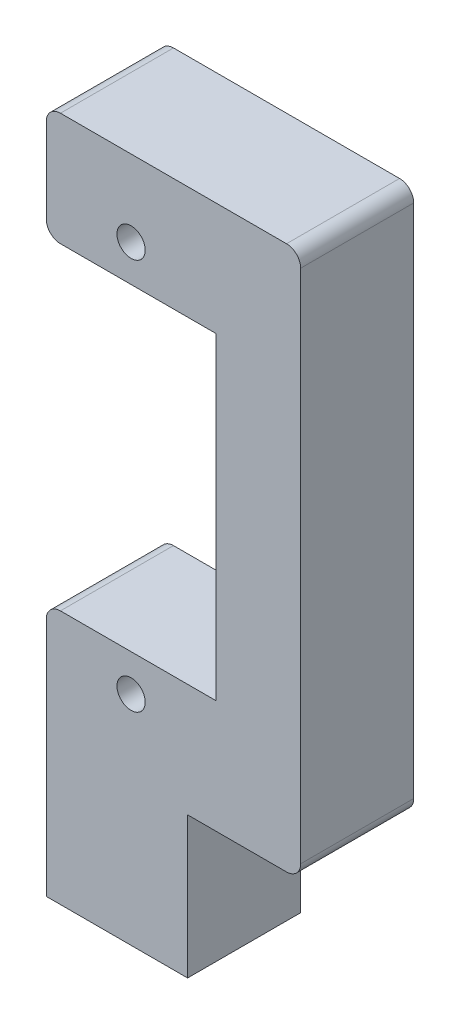
SolidWorks part; units mm, degrees
ref_plane "Front Plane" through (0, 0, 0) normal (0, 0, 1) x (1, 0, 0)
ref_plane "Top Plane" through (0, 0, 0) normal (0, 1, 0) x (1, 0, 0)
ref_plane "Right Plane" through (0, 0, 0) normal (1, 0, 0) x (0, 0, -1)
sketch "Sketch1" plane through (0, 0, 0) normal (0, 0, 1) x (1, 0, 0)
  line L0 (0, 0) -> (0, 10)
  line L1 (8, 48.5) -> (-10, 48.5)
  line L2 (-10, 48.5) -> (-10, 40.5)
  line L3 (-10, 40.5) -> (2, 40.5)
  line L4 (2, 40.5) -> (2, 18)
  line L5 (2, 18) -> (-10, 18)
  line L6 (-10, 18) -> (-10, 10)
  line L7 (0, 10) -> (8, 10)
  line L8 (-10, 10) -> (-10, 0)
  line L9 (-10, 0) -> (0, 0)
  line L10 (8, 10) -> (8, 48.5)
  line L11 (8, 29.25) -> (-17.0252, 29.25) construction
  line L12 (-4, 40.5) -> (-4, 18) construction
  circle A0 centre (-4, 43.1) radius 1
  circle A1 centre (-4, 15.4) radius 1
  dimension "D8" = 13.85
  dimension "D10" = 2
  dimension "D1" = 10
  dimension "D2" = 10
  dimension "D3" = 12
  dimension "D4" = 6
  dimension "D5" = 22.5
  dimension "D6" = 8
  dimension "D7" = 8
  dimension "D9" = 13.85
extrude "Boss-Extrude1" add sketch "Sketch1" along normal blind 8
fillet "Fillet1" radius 1 5 edges at (-10, 40.5, 4) (-10, 18, 4) (8, 10, 4) (-10, 48.5, 4) (8, 48.5, 4)
